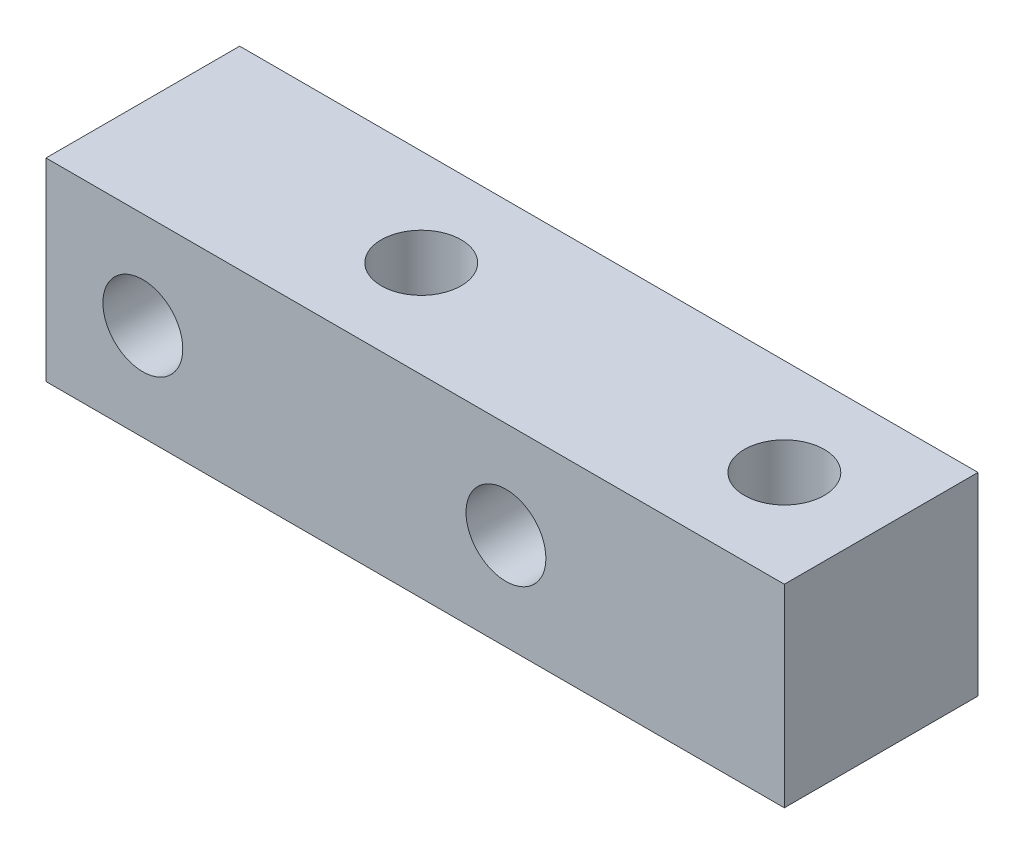
SolidWorks part; units mm, degrees
material "6063-T5"
ref_plane "前视基准面" through (0, 0, 0) normal (0, 0, 1) x (1, 0, 0)
ref_plane "上视基准面" through (0, 0, 0) normal (0, 1, 0) x (1, 0, 0)
ref_plane "右视基准面" through (0, 0, 0) normal (1, 0, 0) x (0, 0, -1)
other "Configuration Table"
sketch "草图1" plane through (0, 0, 0) normal (0, 0, 1) x (1, 0, 0)
  line L1 (-15.25, -4) -> (15.25, -4)
  line L2 (-15.25, -4) -> (-15.25, 4)
  line L3 (-15.25, 4) -> (15.25, 4)
  line L4 (15.25, -4) -> (15.25, 4)
  line L5 (-15.25, -4) -> (15.25, 4) construction
  line L6 (-15.25, 4) -> (15.25, -4) construction
  point P0 (0, 0)
  dimension "D1" = 8
  dimension "D2" = 30.5
extrude "凸台-拉伸1" add sketch "草图1" along normal blind 8
sketch "草图2" plane through (0, 0, 8) normal (0, 0, 1) x (1, 0, 0)
  line L0 (15.25, 4) -> (-15.25, 4) construction
  line L1 (-15.25, 4) -> (-15.25, -4) construction
  circle A0 centre (3.75, 0) radius 2.025
  circle A1 centre (-11.25, 0) radius 2.025
  dimension "D1" = 4.05
  dimension "D3" = 4
  dimension "D4" = 15
  dimension "D2" = 4
hole_wizard "M4 螺纹孔1" positions "3D草图1" profile "草图3" tap size "M4" standard "GB" end condition through all
sketch3d "3D草图1"
  point P0 (3.75, 0, 8)
  point P3 (-11.25, 0, 8)
sketch "草图3" plane through (3.75, 0, 8) normal (1, 0, 0) x (0, -1, 0)
  line L0 (0, 0) -> (0, 8)
  line L1 (0, 8) -> (1.65, 8)
  line L2 (1.65, 8) -> (1.65, 0)
  line L5 (1.65, 0) -> (0, 0)
  line L11 (0, -6.35) -> (0, 107.95) construction
  dimension "通孔螺纹孔钻头直径" = 3.3
  dimension "通孔螺纹孔钻头深度" = 8
cosmetic thread "孔螺蚊线1"
cosmetic thread "孔螺蚊线2"
sketch "草图4" plane through (0, 4, 0) normal (0, 1, 0) x (1, 0, 0)
  line L0 (15.25, -8) -> (15.25, 0) construction
  line L1 (-3.75, -4) -> (15.25, -4) construction
  point P0 (-3.75, -4)
  point P1 (11.25, -4)
  dimension "D1" = 15
  dimension "D2" = 4
hole_wizard "M4 螺纹孔2" positions "3D草图2" profile "草图5" tap size "M4" standard "GB" end condition through all
sketch3d "3D草图2"
  point P0 (-3.75, 4, 4)
  point P3 (11.25, 4, 4)
sketch "草图5" plane through (-3.75, 4, 4) normal (1, 0, 0) x (0, 0, 1)
  line L0 (0, 0) -> (0, 8)
  line L1 (0, 8) -> (1.65, 8)
  line L2 (1.65, 8) -> (1.65, 0)
  line L5 (1.65, 0) -> (0, 0)
  line L11 (0, -6.35) -> (0, 107.95) construction
  dimension "通孔螺纹孔钻头直径" = 3.3
  dimension "通孔螺纹孔钻头深度" = 8
cosmetic thread "孔螺蚊线3"
cosmetic thread "孔螺蚊线4"
